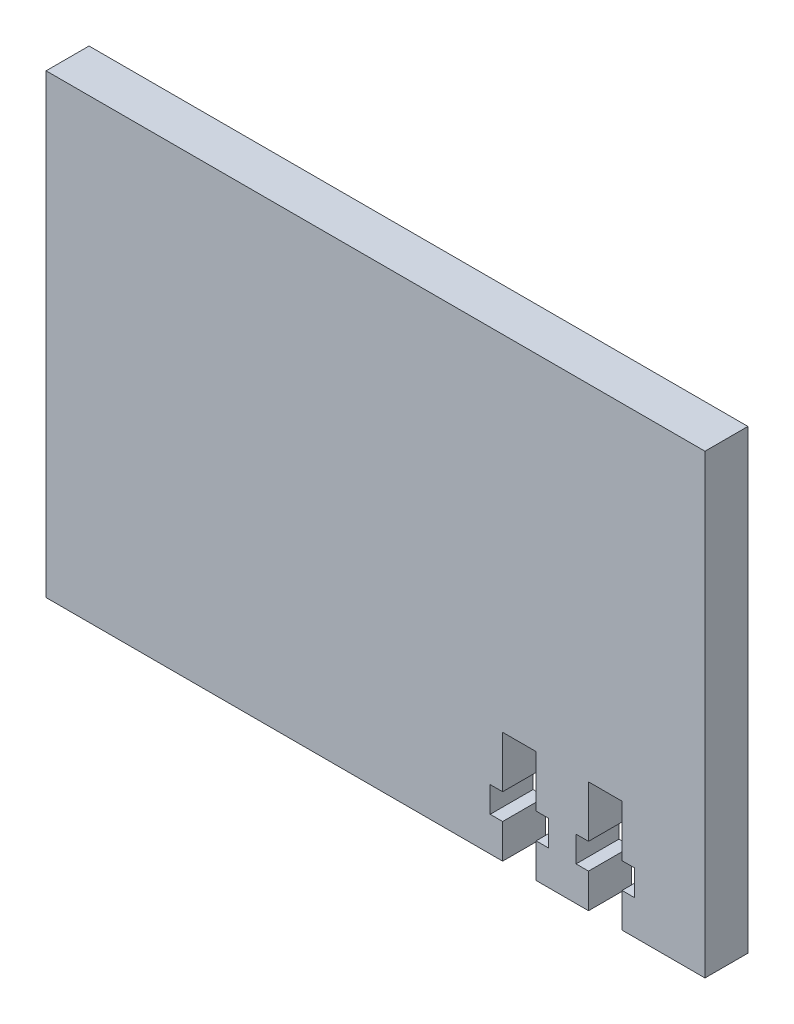
SolidWorks part; units mm, degrees
ref_plane "Front Plane" through (0, 0, 0) normal (0, 0, 1) x (1, 0, 0)
ref_plane "Top Plane" through (0, 0, 0) normal (0, 1, 0) x (1, 0, 0)
ref_plane "Right Plane" through (0, 0, 0) normal (1, 0, 0) x (0, 0, -1)
sketch "Sketch2" plane through (0, 0, 0) normal (0, 0, -1) x (-1, 0, 0)
  line L0 (222.9957, -1.88) -> (222.9957, -55)
  line L1 (222.9957, -1.88) -> (146.2775, -1.88)
  line L2 (222.9957, -55) -> (146.2775, -55)
  line L3 (146.2775, -1.88) -> (146.2775, -55)
  dimension "D1" = 53.12
  dimension "D2" = 76.7182
extrude "Boss-Extrude1" add sketch "Sketch2" along normal blind 5
sketch "Sketch3" plane through (0, 0, -5) normal (0, 0, -1) x (-1, 0, 0)
  line L0 (155.9375, -55) -> (159.8375, -55) construction
  line L1 (155.9375, -55) -> (155.9375, -51)
  line L2 (157.8875, -55) -> (157.8875, -42) construction
  line L3 (155.9375, -42) -> (159.8375, -42)
  line L4 (155.9375, -48) -> (154.4875, -48)
  line L5 (154.4875, -48) -> (154.4875, -51)
  line L6 (155.9375, -51) -> (154.4875, -51)
  line L7 (155.9375, -48) -> (155.9375, -42)
  line L8 (159.8375, -48) -> (159.8375, -42)
  line L9 (159.8375, -51) -> (161.2875, -51)
  line L10 (161.2875, -48) -> (161.2875, -51)
  line L11 (159.8375, -48) -> (161.2875, -48)
  line L12 (159.8375, -55) -> (159.8375, -51)
  line L13 (165.9375, -55) -> (169.8375, -55) construction
  line L14 (165.9375, -55) -> (165.9375, -51)
  line L15 (167.8875, -55) -> (167.8875, -42) construction
  line L16 (165.9375, -42) -> (169.8375, -42)
  line L17 (165.9375, -48) -> (164.4875, -48)
  line L18 (164.4875, -48) -> (164.4875, -51)
  line L19 (165.9375, -51) -> (164.4875, -51)
  line L20 (165.9375, -48) -> (165.9375, -42)
  line L21 (169.8375, -48) -> (169.8375, -42)
  line L22 (169.8375, -51) -> (171.2875, -51)
  line L23 (171.2875, -48) -> (171.2875, -51)
  line L24 (169.8375, -48) -> (171.2875, -48)
  line L25 (169.8375, -55) -> (169.8375, -51)
  line L26 (162.8875, 11.7401) -> (162.8875, -89.703) construction
  line L27 (165.9375, -55) -> (169.8375, -55)
  line L29 (155.9375, -55) -> (159.8375, -55)
  line L31 (146.2775, -55) -> (222.9957, -55) construction
  line L32 (146.2775, -1.88) -> (146.2775, -55) construction
  dimension "D1" = 3.9
  dimension "D2" = 4
  dimension "D3" = 6
  dimension "D4" = 3
  dimension "D5" = 1.45
  dimension "D6" = 3.9
  dimension "D7" = 4
  dimension "D8" = 6
  dimension "D9" = 3
  dimension "D10" = 1.45
  dimension "D11" = 10
  dimension "D12" = 11.61
extrude "Cut-Extrude1" cut sketch "Sketch3" against normal blind 10
